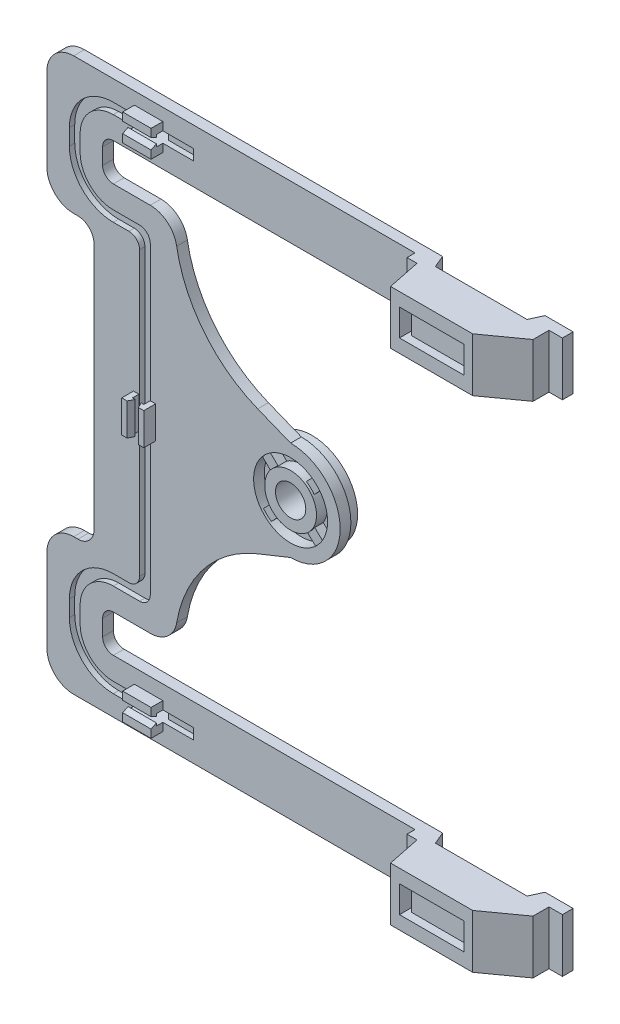
SolidWorks part; units mm, degrees
ref_plane "정면" through (0, 0, 0) normal (1, 0, 0) x (0, 1, 0)
ref_plane "윗면" through (0, 0, 0) normal (0, 0, 1) x (0, 1, 0)
ref_plane "우측면" through (0, 0, 0) normal (0, 1, 0) x (-1, 0, 0)
sketch "스케치1" plane through (0, 0, 0) normal (0, 0, 1) x (0, 1, 0)
  line L0 (0, 51.2656) -> (0, -59.5314) construction
  line L1 (41.5929, -44.9344) -> (51.5929, -44.9344)
  line L2 (51.5929, -44.9344) -> (51.5929, 46.2656)
  line L3 (46.5929, 51.2656) -> (31.1165, 51.2656)
  line L4 (26.1165, 46.2656) -> (26.1165, 45.4722)
  line L5 (23.1165, 42.4722) -> (-23.1165, 42.4722)
  line L6 (41.5929, -44.9344) -> (41.5929, 38.8656)
  line L7 (39.5929, 40.8656) -> (36.5929, 40.8656)
  line L8 (34.5929, 38.8656) -> (34.5929, 32.1656)
  line L9 (9.25, 5.7854) -> (11.7128, 11.9239)
  line L10 (34.5929, 31.9724) -> (34.5929, 32.1656)
  line L11 (-34.5929, 31.9724) -> (-34.5929, 32.1656)
  line L12 (-9.25, 5.7854) -> (-11.7128, 11.9239)
  line L13 (-34.5929, 38.8656) -> (-34.5929, 32.1656)
  line L14 (-39.5929, 40.8656) -> (-36.5929, 40.8656)
  line L15 (-41.5929, -44.9344) -> (-41.5929, 38.8656)
  line L16 (-26.1165, 46.2656) -> (-26.1165, 45.4722)
  line L17 (-46.5929, 51.2656) -> (-31.1165, 51.2656)
  line L18 (-51.5929, -44.9344) -> (-51.5929, 46.2656)
  line L19 (-41.5929, -44.9344) -> (-51.5929, -44.9344)
  arc A0 (11.7128, 11.9239) -> (30.436, 27.044) centre (34.5929, 2.7442) cw
  arc A1 (-9.25, 5.7854) -> (9.25, 5.7854) centre (0, 5.7854) ccw
  arc A2 (-11.7128, 11.9239) -> (-30.436, 27.044) centre (-34.5929, 2.7442) ccw
  arc A3 (30.436, 27.044) -> (34.5929, 31.9724) centre (29.5929, 31.9724) ccw
  arc A4 (-30.436, 27.044) -> (-34.5929, 31.9724) centre (-29.5929, 31.9724) cw
  arc A5 (-26.1165, 46.2656) -> (-31.1165, 51.2656) centre (-31.1165, 46.2656) ccw
  arc A6 (31.1165, 51.2656) -> (26.1165, 46.2656) centre (31.1165, 46.2656) ccw
  arc A7 (51.5929, 46.2656) -> (46.5929, 51.2656) centre (46.5929, 46.2656) ccw
  arc A8 (-46.5929, 51.2656) -> (-51.5929, 46.2656) centre (-46.5929, 46.2656) ccw
  arc A9 (26.1165, 45.4722) -> (23.1165, 42.4722) centre (23.1165, 45.4722) cw
  arc A10 (-26.1165, 45.4722) -> (-23.1165, 42.4722) centre (-23.1165, 45.4722) ccw
  arc A11 (41.5929, 38.8656) -> (39.5929, 40.8656) centre (39.5929, 38.8656) ccw
  arc A12 (36.5929, 40.8656) -> (34.5929, 38.8656) centre (36.5929, 38.8656) ccw
  arc A13 (-34.5929, 38.8656) -> (-36.5929, 40.8656) centre (-36.5929, 38.8656) ccw
  arc A14 (-39.5929, 40.8656) -> (-41.5929, 38.8656) centre (-39.5929, 38.8656) ccw
  point P27 (0, 42.4722)
  point P31 (34.5929, 27.397)
  point P34 (-34.5929, 27.397)
  point P37 (-26.1165, 51.2656)
  point P40 (26.1165, 51.2656)
  point P43 (51.5929, 51.2656)
  point P46 (-51.5929, 51.2656)
  point P49 (26.1165, 42.4722)
  point P52 (-26.1165, 42.4722)
  point P55 (41.5929, 40.8656)
  point P58 (34.5929, 40.8656)
  point P61 (-34.5929, 40.8656)
  point P64 (-41.5929, 40.8656)
  dimension "D7" = 18.5
  dimension "D8" = 5
  dimension "D9" = 3
  dimension "D10" = 2
  dimension "D1" = 96.2
  dimension "D2" = 10
  dimension "D3" = 51.5929
  dimension "D4" = 7
  dimension "D5" = 10.4
  dimension "D6" = 8.7
extrude "보스-돌출1" add sketch "스케치1" along normal blind 2
sketch "스케치3" plane through (0, 0, 2) normal (0, 0, 1) x (1, 0, 0)
  circle A0 centre (-5.7854, 0) radius 2.83
extrude "컷-돌출1" cut sketch "스케치3" against normal blind 2
sketch "스케치4" plane through (0, 0, 2) normal (0, 0, 1) x (1, 0, 0)
  circle A0 centre (-5.7854, 0) radius 2.83
  circle A1 centre (-5.7854, 0) radius 4.83
  circle A2 centre (-5.7854, 0) radius 6.9
  dimension "D1" = 2
extrude "컷-돌출2" cut sketch "스케치4" against normal blind 2 contours A2 A1
sketch "스케치5" plane through (0, 0, 0) normal (0, 0, -1) x (1, 0, 0)
  circle A0 centre (-5.7854, 0) radius 8.5
  dimension "D1" = 17
extrude "보스-돌출2" add sketch "스케치5" along normal blind 2
sketch "스케치6" plane through (0, 0, 0) normal (0, 0, 1) x (1, 0, 0)
  circle A0 centre (-5.7854, 0) radius 2.83
extrude "컷-돌출3" cut sketch "스케치6" against normal through all
sketch "스케치7" plane through (0, 0, 2) normal (0, 0, 1) x (1, 0, 0)
  line L19 (-31.9724, 30.3929) -> (-38.8656, 30.3929) construction
  line L20 (-47.0656, 36.5929) -> (-47.0656, 39.5929)
  line L21 (-38.8656, 47.7929) -> (-23.8656, 47.7929)
  line L22 (-23.8656, -47.7929) -> (-38.8656, -47.7929)
  line L23 (-47.0656, -39.5929) -> (-47.0656, -36.5929)
  line L24 (-38.8656, -30.3929) -> (-31.9724, -30.3929) construction
  line L25 (-31.9724, -28.3929) -> (-31.9724, 28.3929)
  line L26 (-38.8656, -28.3929) -> (-35.9724, -28.3929)
  line L27 (-33.9724, -26.3929) -> (-33.9724, 26.3929)
  line L28 (-35.9724, 28.3929) -> (-38.8656, 28.3929)
  line L29 (-38.8656, -28.3929) -> (-33.9724, -28.3929) construction
  line L30 (-33.9724, -28.3929) -> (-33.9724, 28.3929) construction
  line L31 (-33.9724, 28.3929) -> (-38.8656, 28.3929) construction
  line L32 (-23.8656, 45.7929) -> (-23.8656, 47.7929)
  line L33 (-23.8656, -47.7929) -> (-23.8656, -45.7929)
  line L34 (-38.8656, 45.7929) -> (40.7344, 45.7929)
  line L35 (40.7344, 45.7929) -> (40.7344, 47.3929)
  line L36 (40.7344, 47.3929) -> (-46.2656, 47.3929)
  line L37 (-47.0656, 46.5929) -> (-47.0656, 31.1165)
  line L38 (-46.2656, 30.3165) -> (-45.4722, 30.3165)
  line L39 (-38.2722, 23.1165) -> (-38.2722, -23.1165)
  line L40 (-45.4722, -30.3165) -> (-46.2656, -30.3165)
  line L41 (-47.0656, -31.1165) -> (-47.0656, -46.5929)
  line L42 (-46.2656, -47.3929) -> (40.7344, -47.3929)
  line L43 (40.7344, -47.3929) -> (40.7344, -45.7929)
  line L44 (40.7344, -45.7929) -> (-38.8656, -45.7929)
  line L45 (-45.0656, -39.5929) -> (-45.0656, -36.5929)
  line L46 (-38.8656, -30.3929) -> (-31.9724, -30.3929)
  line L47 (-13.4878, -7.8149) -> (-6.4777, -5.0023)
  line L48 (-6.4777, 5.0023) -> (-13.4878, 7.8149)
  line L49 (-31.9724, 30.3929) -> (-38.8656, 30.3929)
  line L50 (-45.0656, 36.5929) -> (-45.0656, 39.5929)
  line L51 (-38.8656, 45.7929) -> (-23.8656, 45.7929)
  line L61 (-23.8656, -45.7929) -> (-38.8656, -45.7929)
  line L62 (-45.0656, -39.5929) -> (-45.0656, -36.5929)
  line L63 (-38.8656, -30.3929) -> (-33.9724, -30.3929)
  line L66 (-33.9724, 30.3929) -> (-38.8656, 30.3929)
  line L67 (-45.0656, 36.5929) -> (-45.0656, 39.5929)
  line L68 (-31.9724, 28.3929) -> (-38.8656, 28.3929) construction
  line L69 (-38.8656, -28.3929) -> (-31.9724, -28.3929) construction
  arc A15 (-47.0656, 36.5929) -> (-38.8656, 28.3929) centre (-38.8656, 36.5929) ccw
  arc A16 (-38.8656, 47.7929) -> (-47.0656, 39.5929) centre (-38.8656, 39.5929) ccw
  arc A17 (-47.0656, -39.5929) -> (-38.8656, -47.7929) centre (-38.8656, -39.5929) ccw
  arc A18 (-38.8656, -28.3929) -> (-47.0656, -36.5929) centre (-38.8656, -36.5929) ccw
  arc A19 (-31.9724, 28.3929) -> (-33.9724, 30.3929) centre (-33.9724, 28.3929) ccw
  arc A20 (-33.9724, -30.3929) -> (-31.9724, -28.3929) centre (-33.9724, -28.3929) ccw
  arc A21 (-35.9724, 28.3929) -> (-33.9724, 26.3929) centre (-35.9724, 26.3929) cw
  arc A23 (-35.9724, -28.3929) -> (-33.9724, -26.3929) centre (-35.9724, -26.3929) ccw
  arc A30 (-46.2656, 47.3929) -> (-47.0656, 46.5929) centre (-46.2656, 46.5929) ccw
  arc A31 (-47.0656, 31.1165) -> (-46.2656, 30.3165) centre (-46.2656, 31.1165) ccw
  arc A32 (-38.2722, 23.1165) -> (-45.4722, 30.3165) centre (-45.4722, 23.1165) ccw
  arc A33 (-45.4722, -30.3165) -> (-38.2722, -23.1165) centre (-45.4722, -23.1165) ccw
  arc A34 (-46.2656, -30.3165) -> (-47.0656, -31.1165) centre (-46.2656, -31.1165) ccw
  arc A35 (-47.0656, -46.5929) -> (-46.2656, -47.3929) centre (-46.2656, -46.5929) ccw
  arc A36 (-45.0656, -39.5929) -> (-38.8656, -45.7929) centre (-38.8656, -39.5929) ccw
  arc A37 (-38.8656, -30.3929) -> (-45.0656, -36.5929) centre (-38.8656, -36.5929) ccw
  arc A38 (-31.9724, -30.3929) -> (-31.1839, -29.7278) centre (-31.9724, -29.5929) ccw
  arc A39 (-13.4878, -7.8149) -> (-31.1839, -29.7278) centre (-2.7442, -34.5929) ccw
  arc A40 (-6.4777, -5.0023) -> (-6.4777, 5.0023) centre (-5.7854, 0) ccw
  arc A41 (-31.1839, 29.7278) -> (-13.4878, 7.8149) centre (-2.7442, 34.5929) ccw
  arc A42 (-31.1839, 29.7278) -> (-31.9724, 30.3929) centre (-31.9724, 29.5929) ccw
  arc A43 (-45.0656, 36.5929) -> (-38.8656, 30.3929) centre (-38.8656, 36.5929) ccw
  arc A44 (-38.8656, 45.7929) -> (-45.0656, 39.5929) centre (-38.8656, 39.5929) ccw
  arc A51 (-45.0656, -39.5929) -> (-38.8656, -45.7929) centre (-38.8656, -39.5929) ccw
  arc A52 (-38.8656, -30.3929) -> (-45.0656, -36.5929) centre (-38.8656, -36.5929) ccw
  arc A58 (-45.0656, 36.5929) -> (-38.8656, 30.3929) centre (-38.8656, 36.5929) ccw
  arc A59 (-38.8656, 45.7929) -> (-45.0656, 39.5929) centre (-38.8656, 39.5929) ccw
  arc A60 (-33.9724, -28.3929) -> (-33.9724, -28.3929) centre (-33.9724, -28.3929) ccw construction
  arc A61 (-33.9724, 28.3929) -> (-33.9724, 28.3929) centre (-33.9724, 28.3929) ccw construction
  dimension "D4" = 2
  dimension "D6" = 2
  dimension "D7" = 15
  dimension "D8" = 15
  dimension "D1" = 4.2
  dimension "D2" = 2
  dimension "D3" = 2
  dimension "D5" = 2
extrude "컷-돌출4" cut sketch "스케치7" against normal blind 1 contours A59 L51 L32 L21 A16 L20 A15 L28 A21 L27 A23 L26 A18 L23 A17 L22 L33 L61 A51 L62 A52 L63 A20 L25 A19 L66 A58 L67
sketch "스케치8" plane through (0, 0, 0) normal (0, 0, -1) x (1, 0, 0)
  line L0 (-23.8656, 47.7929) -> (-38.8656, 47.7929) construction
  line L1 (-34.9269, 47.7929) -> (-29.5953, 47.7929)
  line L2 (-34.9269, 47.7929) -> (-34.9269, 45.7929)
  line L3 (-34.9269, 45.7929) -> (-29.5953, 45.7929)
  line L4 (-29.5953, 47.7929) -> (-29.5953, 45.7929)
  line L5 (-23.8656, 45.7929) -> (-38.8656, 45.7929) construction
  line L6 (-5.7854, 0) -> (-59.1477, 0) construction
  line L7 (-10.8584, 47.7929) -> (27.377, 47.7929)
  line L8 (-10.8584, 47.7929) -> (-10.8584, 45.7929)
  line L9 (-10.8584, 45.7929) -> (27.377, 45.7929)
  line L10 (27.377, 47.7929) -> (27.377, 45.7929)
  line L11 (27.377, -47.7929) -> (27.377, -45.7929)
  line L12 (-10.8584, -45.7929) -> (27.377, -45.7929)
  line L13 (-10.8584, -47.7929) -> (-10.8584, -45.7929)
  line L14 (-10.8584, -47.7929) -> (27.377, -47.7929)
  line L15 (-29.5953, -47.7929) -> (-29.5953, -45.7929)
  line L16 (-34.9269, -45.7929) -> (-29.5953, -45.7929)
  line L17 (-34.9269, -47.7929) -> (-34.9269, -45.7929)
  line L18 (-34.9269, -47.7929) -> (-29.5953, -47.7929)
extrude "컷-돌출5" cut sketch "스케치8" against normal blind 1
sketch "스케치9" plane through (0, 0, 2) normal (0, 0, 1) x (1, 0, 0)
  line L0 (44.9344, 51.5929) -> (-46.2656, 51.5929) construction
  line L1 (42.4344, 51.5929) -> (17.4344, 51.5929)
  line L2 (42.4344, 51.5929) -> (42.4344, 41.5929)
  line L3 (42.4344, 41.5929) -> (17.4344, 41.5929)
  line L4 (17.4344, 51.5929) -> (17.4344, 41.5929)
  line L5 (-38.8656, 41.5929) -> (44.9344, 41.5929) construction
  line L6 (44.9344, -41.5929) -> (-38.8656, -41.5929) construction
  line L7 (42.4344, -41.5929) -> (17.4344, -41.5929)
  line L8 (42.4344, -41.5929) -> (42.4344, -51.5929)
  line L9 (42.4344, -51.5929) -> (17.4344, -51.5929)
  line L10 (17.4344, -41.5929) -> (17.4344, -51.5929)
  line L11 (-46.2656, -51.5929) -> (44.9344, -51.5929) construction
  line L12 (44.9344, -51.5929) -> (44.9344, -41.5929) construction
  line L13 (44.9344, 41.5929) -> (44.9344, 51.5929) construction
  dimension "D1" = 25
  dimension "D2" = 25
  dimension "D3" = 2.5
  dimension "D4" = 2.5
extrude "보스-돌출3" add sketch "스케치9" along normal blind 7.7
sketch "스케치10" plane through (0, -51.5929, 0) normal (0, -1, 0) x (1, 0, 0)
  line L0 (42.4344, 2) -> (42.4344, 4.9882)
  line L1 (42.4344, 9.7) -> (42.4344, 2) construction
  line L2 (42.4344, 2) -> (44.9344, 2) construction
  line L3 (42.4344, 4.9882) -> (35.8817, 9.7)
  line L4 (17.4344, 9.7) -> (42.4344, 9.7) construction
  line L5 (35.8817, 9.7) -> (20.5687, 9.7)
  line L6 (20.5687, 9.7) -> (19.2988, 3.4941)
  line L7 (19.2988, 3.4941) -> (17.4344, 3.4941)
  line L8 (17.4344, 9.7) -> (17.4344, 2) construction
  line L9 (17.4344, 11.6363) -> (42.4344, 11.6363)
  line L10 (42.4344, 11.6363) -> (42.4344, 4.9882)
  line L11 (17.4344, 11.6363) -> (17.4344, 3.4941)
  line L12 (20.5687, 0) -> (21.5397, 2.3)
  line L13 (-46.2656, 0) -> (44.9344, 0) construction
  line L14 (21.5397, 2.3) -> (38.6455, 2.3)
  line L15 (38.6455, 2.3) -> (39.6913, 0)
  line L16 (39.6913, 0) -> (39.6913, -1.6599)
  line L17 (39.6913, -1.6599) -> (20.5687, -1.6599)
  line L18 (20.5687, -1.6599) -> (20.5687, 0)
  line M14 (-46.2656, 0) -> (44.9344, 0)
  line M17 (42.4344, 2) -> (42.4344, 9.7)
  line M18 (42.4344, 9.7) -> (17.4344, 9.7)
  line M19 (17.4344, 9.7) -> (17.4344, 2)
  dimension "D1" = 2.3
extrude "컷-돌출6" cut sketch "스케치10" against normal through all and the other way through all contours L9 L11 L10 M18 | L7 L6 M18 M19 | L3 M17 M18 | L18 L17 L16 M14 | L15 L14 L12 M14
sketch "스케치13" plane through (0, 0, 2.3) normal (0, 0, -1) x (1, 0, 0)
  line L1 (21.5397, -41.5929) -> (21.5397, -51.5929) construction
  line L3 (38.6455, -51.5929) -> (38.6455, -41.5929) construction
  line L5 (21.5397, 51.5929) -> (21.5397, 41.5929) construction
  line L7 (38.6455, 41.5929) -> (38.6455, 51.5929) construction
  line L9 (21.5397, -43.5929) -> (21.5397, -49.5929)
  line L11 (38.6455, -49.5929) -> (38.6455, -43.5929)
  line L13 (21.5397, 49.5929) -> (21.5397, 43.5929)
  line L15 (38.6455, 43.5929) -> (38.6455, 49.5929)
  line L16 (36.6455, 49.5929) -> (23.5397, 49.5929)
  line L18 (23.5397, 43.5929) -> (36.6455, 43.5929)
  line L20 (36.6455, -43.5929) -> (23.5397, -43.5929)
  line L22 (23.5397, -49.5929) -> (36.6455, -49.5929)
  line L24 (23.5397, 49.5929) -> (23.5397, 43.5929) construction
  line L25 (36.6455, 43.5929) -> (36.6455, 49.5929) construction
  line L26 (21.5397, 49.5929) -> (23.5397, 49.5929)
  line L27 (36.6455, 49.5929) -> (38.6455, 49.5929)
  line L28 (36.6455, 43.5929) -> (38.6455, 43.5929)
  line L29 (23.5397, 43.5929) -> (21.5397, 43.5929)
  line L30 (36.6455, -43.5929) -> (38.6455, -43.5929)
  line L31 (36.6455, -49.5929) -> (38.6455, -49.5929)
  line L32 (23.5397, -49.5929) -> (21.5397, -49.5929)
  line L33 (23.5397, -43.5929) -> (21.5397, -43.5929)
  line L34 (38.6455, -51.5929) -> (38.6455, -41.5929) construction
  line L35 (21.5397, -41.5929) -> (21.5397, -51.5929) construction
  line L36 (23.5397, -43.5929) -> (23.5397, -49.5929) construction
  line L37 (36.6455, -49.5929) -> (36.6455, -43.5929) construction
  line L38 (38.6455, -41.5929) -> (21.5397, -41.5929) construction
  line L39 (21.5397, -51.5929) -> (38.6455, -51.5929) construction
  line L40 (38.6455, 51.5929) -> (21.5397, 51.5929) construction
  line L41 (21.5397, 51.5929) -> (21.5397, 41.5929) construction
  line L42 (21.5397, 41.5929) -> (38.6455, 41.5929) construction
  line L43 (38.6455, 41.5929) -> (38.6455, 51.5929) construction
  dimension "D1" = 2
extrude "컷-돌출7" cut sketch "스케치13" against normal blind 5
sketch "스케치14" plane through (0, 0, 9.7) normal (0, 0, 1) x (1, 0, 0)
  line L0 (-5.7854, 0) -> (36.2123, 0) construction
  line L1 (22.232, 49.1002) -> (34.232, 49.1002)
  line L2 (22.232, 49.1002) -> (22.232, 44.1002)
  line L3 (22.232, 44.1002) -> (34.232, 44.1002)
  line L4 (34.232, 49.1002) -> (34.232, 44.1002)
  line L5 (22.232, 49.1002) -> (34.232, 44.1002) construction
  line L6 (22.232, 44.1002) -> (34.232, 49.1002) construction
  line L7 (22.232, -44.1002) -> (34.232, -49.1002) construction
  line L8 (22.232, -49.1002) -> (34.232, -44.1002) construction
  line L9 (34.232, -49.1002) -> (34.232, -44.1002)
  line L10 (22.232, -44.1002) -> (34.232, -44.1002)
  line L11 (22.232, -49.1002) -> (22.232, -44.1002)
  line L12 (22.232, -49.1002) -> (34.232, -49.1002)
  point P0 (28.232, 46.6002)
  point P13 (28.232, -46.6002)
  dimension "D1" = 5
  dimension "D2" = 12
extrude "컷-돌출8" cut sketch "스케치14" against normal blind 1.5
sketch "스케치15" plane through (0, 0, 8.2) normal (0, 0, 1) x (1, 0, 0)
  line L0 (22.232, 44.1002) -> (34.232, 44.1002) construction
  line L1 (22.232, 49.1002) -> (22.982, 49.1002)
  line L2 (22.232, 49.1002) -> (22.232, 44.1002)
  line L3 (22.232, 44.1002) -> (22.982, 44.1002)
  line L4 (22.982, 49.1002) -> (22.982, 44.1002)
  line L5 (-5.7854, 0) -> (56.8372, 0) construction
  line L6 (34.232, 49.1002) -> (33.482, 49.1002)
  line L7 (34.232, 49.1002) -> (34.232, 44.1002)
  line L8 (34.232, 44.1002) -> (33.482, 44.1002)
  line L9 (33.482, 49.1002) -> (33.482, 44.1002)
  line L10 (33.482, -49.1002) -> (33.482, -44.1002)
  line L11 (34.232, -44.1002) -> (33.482, -44.1002)
  line L12 (34.232, -49.1002) -> (34.232, -44.1002)
  line L13 (34.232, -49.1002) -> (33.482, -49.1002)
  line L14 (22.982, -49.1002) -> (22.982, -44.1002)
  line L15 (22.232, -44.1002) -> (22.982, -44.1002)
  line L16 (22.232, -49.1002) -> (22.232, -44.1002)
  line L17 (22.232, -49.1002) -> (22.982, -49.1002)
  dimension "D1" = 0.75
  dimension "D2" = 0.75
extrude "컷-돌출9" cut sketch "스케치15" against normal through all
sketch "스케치16" plane through (0, 0, 2) normal (0, 0, 1) x (1, 0, 0)
  line L0 (-5.7854, 0) -> (-99.9412, 0) construction
  line L1 (-34.9269, 47.7929) -> (-29.6269, 47.7929)
  line L2 (-34.9269, 47.7929) -> (-34.9269, 49.2929)
  line L3 (-34.9269, 49.2929) -> (-29.6269, 49.2929)
  line L4 (-29.6269, 47.7929) -> (-29.6269, 49.2929)
  line L5 (-34.9269, 45.7929) -> (-29.6269, 45.7929)
  line L6 (-34.9269, 45.7929) -> (-34.9269, 44.2929)
  line L7 (-34.9269, 44.2929) -> (-29.6269, 44.2929)
  line L8 (-29.6269, 45.7929) -> (-29.6269, 44.2929)
  line L9 (-29.6269, -45.7929) -> (-29.6269, -44.2929)
  line L10 (-34.9269, -44.2929) -> (-29.6269, -44.2929)
  line L11 (-34.9269, -45.7929) -> (-34.9269, -44.2929)
  line L12 (-34.9269, -45.7929) -> (-29.6269, -45.7929)
  line L13 (-29.6269, -47.7929) -> (-29.6269, -49.2929)
  line L14 (-34.9269, -49.2929) -> (-29.6269, -49.2929)
  line L15 (-34.9269, -47.7929) -> (-34.9269, -49.2929)
  line L16 (-34.9269, -47.7929) -> (-29.6269, -47.7929)
  dimension "D1" = 1.5
  dimension "D2" = 1.5
  dimension "D3" = 5.3
  dimension "D4" = 5.3
extrude "보스-돌출4" add sketch "스케치16" along normal blind 2.2
sketch "스케치17" plane through (-34.9269, 0, 0) normal (-1, 0, 0) x (0, -1, 0)
  line L0 (-47.7929, 4.2) -> (-47.2929, 3.2)
  line L1 (-49.2929, 4.2) -> (-47.7929, 4.2) construction
  line L2 (-47.2929, 3.2) -> (-47.7929, 3.2)
  line L3 (-47.7929, 4.2) -> (-47.7929, 2) construction
  line L4 (-47.7929, 3.2) -> (-47.7929, 4.2)
  line L5 (-45.7929, 4.2) -> (-46.2929, 3.2)
  line L6 (-45.7929, 4.2) -> (-45.7929, 2) construction
  line L7 (-46.2929, 3.2) -> (-45.7929, 3.2)
  line L8 (-45.7929, 3.2) -> (-45.7929, 4.2)
  line L9 (45.7929, 4.2) -> (46.2929, 3.2)
  line L10 (46.2929, 3.2) -> (45.7929, 3.2)
  line L11 (45.7929, 4.2) -> (45.7929, 2) construction
  line L12 (45.7929, 3.2) -> (45.7929, 4.2)
  line L13 (47.7929, 4.2) -> (47.7929, 3.2)
  line L14 (47.7929, 4.2) -> (47.7929, 2) construction
  line L15 (47.7929, 3.2) -> (47.2929, 3.2)
  line L16 (47.2929, 3.2) -> (47.7929, 4.2)
  line L17 (-45.7929, 4.2) -> (-44.2929, 4.2) construction
  dimension "D1" = 0.5
  dimension "D2" = 0.5
  dimension "D3" = 1
  dimension "D4" = 1
  dimension "D5" = 0.5
  dimension "D6" = 0.5
  dimension "D7" = 1
  dimension "D8" = 1
  dimension "D9" = 0
extrude "보스-돌출5" add sketch "스케치17" against normal up to surface (5.3 mm away) up to face at (-29.6269, 48.5429, 3.1)
sketch "스케치18" plane through (0, 0, 2) normal (0, 0, 1) x (1, 0, 0)
  line L0 (-5.7854, 0) -> (-57.4452, 0) construction
  line L1 (-31.9724, -28.3929) -> (-31.9724, 28.3929) construction
  line L2 (-30.9724, 3) -> (-31.9724, 3)
  line L3 (-30.9724, 3) -> (-30.9724, -3)
  line L4 (-30.9724, -3) -> (-31.9724, -3)
  line L5 (-31.9724, 3) -> (-31.9724, -3)
  line L6 (-30.9724, 3) -> (-31.9724, -3) construction
  line L7 (-30.9724, -3) -> (-31.9724, 3) construction
  line L8 (-33.0351, 0) -> (-33.0351, 6.5406) construction
  line L9 (-35.0978, -3) -> (-34.0978, -3)
  line L10 (-34.0978, 3) -> (-34.0978, -3)
  line L11 (-35.0978, 3) -> (-34.0978, 3)
  line L12 (-35.0978, 3) -> (-35.0978, -3)
  point P4 (-31.4724, 0)
  dimension "D1" = 1
  dimension "D2" = 6
extrude "보스-돌출6" add sketch "스케치18" along normal blind 2.2 contours L9 L10 L11 L12 | L3 L2 L5 L4
sketch "스케치19" plane through (0, -3, 0) normal (0, -1, 0) x (1, 0, 0)
  line L0 (-31.9724, 4.2) -> (-32.4724, 3.2)
  line L1 (-32.4724, 3.2) -> (-31.9724, 3.2)
  line L3 (-31.9724, 3.2) -> (-31.9724, 4.2)
  line L4 (-34.0978, 4.2) -> (-34.0978, 3.2)
  line L5 (-34.0978, 4.2) -> (-34.0978, 2) construction
  line L6 (-34.0978, 3.2) -> (-33.5978, 3.2)
  line L7 (-33.5978, 3.2) -> (-34.0978, 4.2)
  dimension "D1" = 0.5
  dimension "D2" = 0.5
  dimension "D3" = 1
  dimension "D4" = 1
extrude "보스-돌출7" add sketch "스케치19" against normal up to surface (6 mm away) up to face at (-31.4724, 3, 3.1)
sketch "스케치20" plane through (0, 0, 0) normal (0, 0, 1) x (1, 0, 0)
  line L0 (-10.7691, 4.7721) -> (-7.8387, 1.9662) construction
  line L1 (-4.3737, 0.0306) -> (-4.3715, 0.0307) construction
  line L2 (-10.5586, -4.9826) -> (-7.7527, -2.0523) construction
  line L3 (-9.7861, -5.6218) -> (-6.9051, -2.6131)
  line L4 (-11.2303, -4.2382) -> (-8.3489, -1.229)
  line L5 (-11.4607, 4.0498) -> (-8.3991, 1.1182)
  line L6 (-10.0775, 5.4944) -> (-7.0159, 2.5628)
  line L7 (-12.5493, -5.6156) -> (0.6402, 8.1586) construction
  line L8 (-11.827, -6.3073) -> (1.3624, 7.467) construction
  line L9 (-11.1047, -6.9989) -> (2.0847, 6.7754) construction
  line L10 (-6.5088, 0.6927) -> (-5.8172, 1.415)
  line L13 (-4.5549, -2.5628) -> (-1.4933, -5.4944)
  line L14 (-11.4607, 4.0498) -> (-1.4933, -5.4944) construction
  line L15 (-3.732, -1.9662) -> (-0.8017, -4.7721) construction
  line L16 (-10.7691, 4.7721) -> (-0.8017, -4.7721) construction
  line L17 (-3.1717, -1.1182) -> (-0.1101, -4.0498)
  line L18 (-10.0775, 5.4944) -> (-0.1101, -4.0498) construction
  line L19 (-2.9432, 0.0616) -> (7.0846, 0.2791) construction
  line L20 (-3.2233, 1.232) -> (-0.3424, 4.2407)
  line L21 (-3.8203, 2.0544) -> (-1.0144, 4.9848) construction
  line L22 (-4.6687, 2.6144) -> (-1.7872, 5.6236)
  line L23 (-4.3726, 0.0317) -> (-4.3715, 0.0307)
  line L26 (-4.3737, 0.0306) -> (-4.3726, 0.0317)
  circle A0 centre (-5.7854, 0) radius 6.9 construction
  circle A1 centre (-5.7854, 0) radius 2.8429
  arc A2 (-11.2303, -4.2382) -> (-9.7861, -5.6218) centre (-5.7854, 0) ccw
  arc A3 (-10.0248, 5.444) -> (-11.4081, 3.9994) centre (-5.7854, 0) ccw
  arc A4 (-0.3424, 4.2407) -> (-1.7872, 5.6236) centre (-5.7854, 0) ccw
  arc A5 (-1.5459, -5.444) -> (-0.1627, -3.9994) centre (-5.7854, 0) ccw
  circle M5 centre (-5.7854, 0) radius 4.83
  circle M6 centre (-5.7854, 0) radius 6.9
  dimension "D1" = 45
  dimension "D2" = 90
  dimension "D3" = 1
  dimension "D4" = 1
  dimension "D5" = 1
  dimension "D6" = 1
extrude "보스-돌출8" add sketch "스케치20" along normal blind 1.6 contours L6 L5 M6 M5 | L22 L20 M5 M6 | L17 L13 M5 M6 | L4 L3 M6 M5
